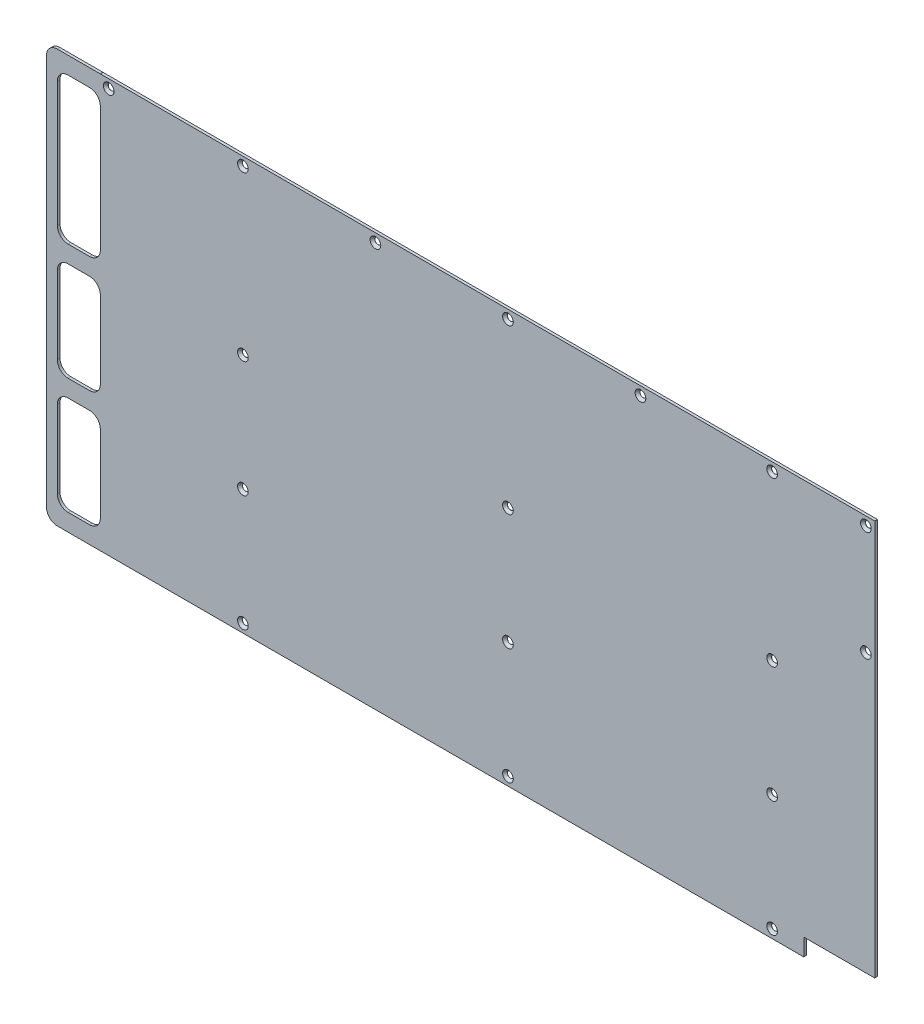
SolidWorks part; units mm, degrees
ref_plane "Front Plane" through (0, 0, 0) normal (0, 0, 1) x (1, 0, 0)
ref_plane "Top Plane" through (0, 0, 0) normal (0, 1, 0) x (1, 0, 0)
ref_plane "Right Plane" through (0, 0, 0) normal (1, 0, 0) x (0, 0, -1)
sketch "Model" plane through (0, 0, 0) normal (0, 0, 1) x (1, 0, 0)
  line L0 (0.1482, 0) -> (415.4382, 0)
  line L1 (415.4382, 0) -> (415.4382, 10.16)
  line L2 (415.4382, 10.16) -> (457.3482, 10.16)
  line L3 (457.3482, 10.16) -> (457.3482, 243.84)
  line L4 (457.3482, 243.84) -> (0.1482, 243.84)
  line L5 (0.1482, 243.84) -> (0.1482, 243.7765)
  line L6 (0.1482, 227.33) -> (0.1482, 153.67)
  line L7 (0.1482, 243.84) -> (-25.2518, 243.84)
  line L8 (0.1482, 243.84) -> (0.1482, 243.7765)
  line L9 (0.1482, 0) -> (-25.2518, 0)
  line L10 (-31.6018, 237.49) -> (-31.6018, 6.35)
  line L11 (-6.2018, 233.68) -> (-18.9018, 233.68)
  line L12 (0.1482, 233.68) -> (0.1482, 147.32)
  line L13 (-6.2018, 147.32) -> (-18.9018, 147.32)
  line L14 (-25.2518, 227.33) -> (-25.2518, 153.67)
  line L15 (-6.2018, 137.16) -> (-18.9018, 137.16)
  line L16 (0.1482, 130.81) -> (0.1482, 85.09)
  line L17 (-6.2018, 78.74) -> (-18.9018, 78.74)
  line L18 (-25.2518, 130.81) -> (-25.2518, 85.09)
  line L19 (-6.2018, 68.58) -> (-18.9018, 68.58)
  line L20 (0.1482, 62.23) -> (0.1482, 16.51)
  line L21 (-6.2018, 10.16) -> (-18.9018, 10.16)
  line L22 (-25.2518, 62.23) -> (-25.2518, 16.51)
  line L23 (0.1482, 233.68) -> (0.1482, 147.32)
  line L24 (0.1482, 137.16) -> (0.1482, 78.74)
  line L25 (0.1482, 137.16) -> (0.1482, 78.74)
  line L26 (0.1482, 68.58) -> (0.1482, 10.16)
  line L27 (0.1482, 68.58) -> (0.1482, 10.16)
  line L276 (452.12, 173.736) -> (452.12, 174.244)
  line L277 (451.866, 173.99) -> (452.374, 173.99)
  line L278 (452.12, 173.736) -> (452.12, 174.244)
  line L279 (451.866, 173.99) -> (452.374, 173.99)
  line L280 (452.12, 173.736) -> (452.12, 174.244)
  line L281 (451.866, 173.99) -> (452.374, 173.99)
  line L282 (452.12, 173.736) -> (452.12, 174.244)
  line L283 (451.866, 173.99) -> (452.374, 173.99)
  line L284 (452.12, 173.736) -> (452.12, 174.244)
  line L285 (451.866, 173.99) -> (452.374, 173.99)
  line L286 (452.12, 173.736) -> (452.12, 174.244)
  line L287 (451.866, 173.99) -> (452.374, 173.99)
  line L288 (452.12, 173.736) -> (452.12, 174.244)
  line L289 (451.866, 173.99) -> (452.374, 173.99)
  line L290 (452.12, 173.736) -> (452.12, 174.244)
  line L291 (451.866, 173.99) -> (452.374, 173.99)
  line L292 (452.12, 238.506) -> (452.12, 239.014)
  line L293 (451.866, 238.76) -> (452.374, 238.76)
  line L294 (452.12, 238.506) -> (452.12, 239.014)
  line L295 (451.866, 238.76) -> (452.374, 238.76)
  line L296 (452.12, 238.506) -> (452.12, 239.014)
  line L297 (451.866, 238.76) -> (452.374, 238.76)
  line L298 (452.12, 238.506) -> (452.12, 239.014)
  line L299 (451.866, 238.76) -> (452.374, 238.76)
  line L300 (452.12, 238.506) -> (452.12, 239.014)
  line L301 (451.866, 238.76) -> (452.374, 238.76)
  line L302 (452.12, 238.506) -> (452.12, 239.014)
  line L303 (451.866, 238.76) -> (452.374, 238.76)
  line L304 (452.12, 238.506) -> (452.12, 239.014)
  line L305 (451.866, 238.76) -> (452.374, 238.76)
  line L306 (452.12, 238.506) -> (452.12, 239.014)
  line L307 (451.866, 238.76) -> (452.374, 238.76)
  line L356 (5.08, 238.506) -> (5.08, 239.014)
  line L357 (4.826, 238.76) -> (5.334, 238.76)
  line L358 (5.08, 238.506) -> (5.08, 239.014)
  line L359 (4.826, 238.76) -> (5.334, 238.76)
  line L360 (5.08, 238.506) -> (5.08, 239.014)
  line L361 (4.826, 238.76) -> (5.334, 238.76)
  line L362 (5.08, 238.506) -> (5.08, 239.014)
  line L363 (4.826, 238.76) -> (5.334, 238.76)
  line L364 (5.08, 238.506) -> (5.08, 239.014)
  line L365 (4.826, 238.76) -> (5.334, 238.76)
  line L366 (5.08, 238.506) -> (5.08, 239.014)
  line L367 (4.826, 238.76) -> (5.334, 238.76)
  line L368 (5.08, 238.506) -> (5.08, 239.014)
  line L369 (4.826, 238.76) -> (5.334, 238.76)
  line L370 (5.08, 238.506) -> (5.08, 239.014)
  line L371 (4.826, 238.76) -> (5.334, 238.76)
  line L372 (84.328, 4.826) -> (84.328, 5.334)
  line L373 (84.074, 5.08) -> (84.582, 5.08)
  line L374 (84.328, 4.826) -> (84.328, 5.334)
  line L375 (84.074, 5.08) -> (84.582, 5.08)
  line L376 (84.328, 4.826) -> (84.328, 5.334)
  line L377 (84.074, 5.08) -> (84.582, 5.08)
  line L378 (84.328, 4.826) -> (84.328, 5.334)
  line L379 (84.074, 5.08) -> (84.582, 5.08)
  line L380 (84.328, 4.826) -> (84.328, 5.334)
  line L381 (84.074, 5.08) -> (84.582, 5.08)
  line L382 (84.328, 4.826) -> (84.328, 5.334)
  line L383 (84.074, 5.08) -> (84.582, 5.08)
  line L384 (84.328, 4.826) -> (84.328, 5.334)
  line L385 (84.074, 5.08) -> (84.582, 5.08)
  line L386 (84.328, 4.826) -> (84.328, 5.334)
  line L387 (84.074, 5.08) -> (84.582, 5.08)
  line L388 (84.328, 73.406) -> (84.328, 73.914)
  line L389 (84.074, 73.66) -> (84.582, 73.66)
  line L390 (84.328, 73.406) -> (84.328, 73.914)
  line L391 (84.074, 73.66) -> (84.582, 73.66)
  line L392 (84.328, 73.406) -> (84.328, 73.914)
  line L393 (84.074, 73.66) -> (84.582, 73.66)
  line L394 (84.328, 73.406) -> (84.328, 73.914)
  line L395 (84.074, 73.66) -> (84.582, 73.66)
  line L396 (84.328, 73.406) -> (84.328, 73.914)
  line L397 (84.074, 73.66) -> (84.582, 73.66)
  line L398 (84.328, 73.406) -> (84.328, 73.914)
  line L399 (84.074, 73.66) -> (84.582, 73.66)
  line L400 (84.328, 73.406) -> (84.328, 73.914)
  line L401 (84.074, 73.66) -> (84.582, 73.66)
  line L402 (84.328, 73.406) -> (84.328, 73.914)
  line L403 (84.074, 73.66) -> (84.582, 73.66)
  line L404 (84.328, 141.986) -> (84.328, 142.494)
  line L405 (84.074, 142.24) -> (84.582, 142.24)
  line L406 (84.328, 141.986) -> (84.328, 142.494)
  line L407 (84.074, 142.24) -> (84.582, 142.24)
  line L408 (84.328, 141.986) -> (84.328, 142.494)
  line L409 (84.074, 142.24) -> (84.582, 142.24)
  line L410 (84.328, 141.986) -> (84.328, 142.494)
  line L411 (84.074, 142.24) -> (84.582, 142.24)
  line L412 (84.328, 141.986) -> (84.328, 142.494)
  line L413 (84.074, 142.24) -> (84.582, 142.24)
  line L414 (84.328, 141.986) -> (84.328, 142.494)
  line L415 (84.074, 142.24) -> (84.582, 142.24)
  line L416 (84.328, 141.986) -> (84.328, 142.494)
  line L417 (84.074, 142.24) -> (84.582, 142.24)
  line L418 (84.328, 141.986) -> (84.328, 142.494)
  line L419 (84.074, 142.24) -> (84.582, 142.24)
  line L420 (84.328, 238.506) -> (84.328, 239.014)
  line L421 (84.074, 238.76) -> (84.582, 238.76)
  line L422 (84.328, 238.506) -> (84.328, 239.014)
  line L423 (84.074, 238.76) -> (84.582, 238.76)
  line L424 (84.328, 238.506) -> (84.328, 239.014)
  line L425 (84.074, 238.76) -> (84.582, 238.76)
  line L426 (84.328, 238.506) -> (84.328, 239.014)
  line L427 (84.074, 238.76) -> (84.582, 238.76)
  line L428 (84.328, 238.506) -> (84.328, 239.014)
  line L429 (84.074, 238.76) -> (84.582, 238.76)
  line L430 (84.328, 238.506) -> (84.328, 239.014)
  line L431 (84.074, 238.76) -> (84.582, 238.76)
  line L432 (84.328, 238.506) -> (84.328, 239.014)
  line L433 (84.074, 238.76) -> (84.582, 238.76)
  line L434 (84.328, 238.506) -> (84.328, 239.014)
  line L435 (84.074, 238.76) -> (84.582, 238.76)
  line L484 (162.56, 238.506) -> (162.56, 239.014)
  line L485 (162.306, 238.76) -> (162.814, 238.76)
  line L486 (162.56, 238.506) -> (162.56, 239.014)
  line L487 (162.306, 238.76) -> (162.814, 238.76)
  line L488 (162.56, 238.506) -> (162.56, 239.014)
  line L489 (162.306, 238.76) -> (162.814, 238.76)
  line L490 (162.56, 238.506) -> (162.56, 239.014)
  line L491 (162.306, 238.76) -> (162.814, 238.76)
  line L492 (162.56, 238.506) -> (162.56, 239.014)
  line L493 (162.306, 238.76) -> (162.814, 238.76)
  line L494 (162.56, 238.506) -> (162.56, 239.014)
  line L495 (162.306, 238.76) -> (162.814, 238.76)
  line L496 (162.56, 238.506) -> (162.56, 239.014)
  line L497 (162.306, 238.76) -> (162.814, 238.76)
  line L498 (162.56, 238.506) -> (162.56, 239.014)
  line L499 (162.306, 238.76) -> (162.814, 238.76)
  line L500 (240.7699, 4.827) -> (240.8141, 5.333)
  line L501 (240.539, 5.1021) -> (241.045, 5.0579)
  line L502 (240.7699, 4.827) -> (240.8141, 5.333)
  line L503 (240.539, 5.1021) -> (241.045, 5.0579)
  line L504 (240.7699, 4.827) -> (240.8141, 5.333)
  line L505 (240.539, 5.1021) -> (241.045, 5.0579)
  line L506 (240.7699, 4.827) -> (240.8141, 5.333)
  line L507 (240.539, 5.1021) -> (241.045, 5.0579)
  line L508 (240.7699, 4.827) -> (240.8141, 5.333)
  line L509 (240.539, 5.1021) -> (241.045, 5.0579)
  line L510 (240.7699, 4.827) -> (240.8141, 5.333)
  line L511 (240.539, 5.1021) -> (241.045, 5.0579)
  line L512 (240.7699, 4.827) -> (240.8141, 5.333)
  line L513 (240.539, 5.1021) -> (241.045, 5.0579)
  line L514 (240.7699, 4.827) -> (240.8141, 5.333)
  line L515 (240.539, 5.1021) -> (241.045, 5.0579)
  line L516 (240.792, 73.406) -> (240.792, 73.914)
  line L517 (240.538, 73.66) -> (241.046, 73.66)
  line L518 (240.792, 73.406) -> (240.792, 73.914)
  line L519 (240.538, 73.66) -> (241.046, 73.66)
  line L520 (240.792, 73.406) -> (240.792, 73.914)
  line L521 (240.538, 73.66) -> (241.046, 73.66)
  line L522 (240.792, 73.406) -> (240.792, 73.914)
  line L523 (240.538, 73.66) -> (241.046, 73.66)
  line L524 (240.792, 73.406) -> (240.792, 73.914)
  line L525 (240.538, 73.66) -> (241.046, 73.66)
  line L526 (240.792, 73.406) -> (240.792, 73.914)
  line L527 (240.538, 73.66) -> (241.046, 73.66)
  line L528 (240.792, 73.406) -> (240.792, 73.914)
  line L529 (240.538, 73.66) -> (241.046, 73.66)
  line L530 (240.792, 73.406) -> (240.792, 73.914)
  line L531 (240.538, 73.66) -> (241.046, 73.66)
  line L532 (240.792, 141.986) -> (240.792, 142.494)
  line L533 (240.538, 142.24) -> (241.046, 142.24)
  line L534 (240.792, 141.986) -> (240.792, 142.494)
  line L535 (240.538, 142.24) -> (241.046, 142.24)
  line L536 (240.792, 141.986) -> (240.792, 142.494)
  line L537 (240.538, 142.24) -> (241.046, 142.24)
  line L538 (240.792, 141.986) -> (240.792, 142.494)
  line L539 (240.538, 142.24) -> (241.046, 142.24)
  line L540 (240.792, 141.986) -> (240.792, 142.494)
  line L541 (240.538, 142.24) -> (241.046, 142.24)
  line L542 (240.792, 141.986) -> (240.792, 142.494)
  line L543 (240.538, 142.24) -> (241.046, 142.24)
  line L544 (240.792, 141.986) -> (240.792, 142.494)
  line L545 (240.538, 142.24) -> (241.046, 142.24)
  line L546 (240.792, 141.986) -> (240.792, 142.494)
  line L547 (240.538, 142.24) -> (241.046, 142.24)
  line L548 (240.792, 238.506) -> (240.792, 239.014)
  line L549 (240.538, 238.76) -> (241.046, 238.76)
  line L550 (240.792, 238.506) -> (240.792, 239.014)
  line L551 (240.538, 238.76) -> (241.046, 238.76)
  line L552 (240.792, 238.506) -> (240.792, 239.014)
  line L553 (240.538, 238.76) -> (241.046, 238.76)
  line L554 (240.792, 238.506) -> (240.792, 239.014)
  line L555 (240.538, 238.76) -> (241.046, 238.76)
  line L556 (240.792, 238.506) -> (240.792, 239.014)
  line L557 (240.538, 238.76) -> (241.046, 238.76)
  line L558 (240.792, 238.506) -> (240.792, 239.014)
  line L559 (240.538, 238.76) -> (241.046, 238.76)
  line L560 (240.792, 238.506) -> (240.792, 239.014)
  line L561 (240.538, 238.76) -> (241.046, 238.76)
  line L562 (240.792, 238.506) -> (240.792, 239.014)
  line L563 (240.538, 238.76) -> (241.046, 238.76)
  line L612 (319.024, 238.506) -> (319.024, 239.014)
  line L613 (318.77, 238.76) -> (319.278, 238.76)
  line L614 (319.024, 238.506) -> (319.024, 239.014)
  line L615 (318.77, 238.76) -> (319.278, 238.76)
  line L616 (319.024, 238.506) -> (319.024, 239.014)
  line L617 (318.77, 238.76) -> (319.278, 238.76)
  line L618 (319.024, 238.506) -> (319.024, 239.014)
  line L619 (318.77, 238.76) -> (319.278, 238.76)
  line L620 (319.024, 238.506) -> (319.024, 239.014)
  line L621 (318.77, 238.76) -> (319.278, 238.76)
  line L622 (319.024, 238.506) -> (319.024, 239.014)
  line L623 (318.77, 238.76) -> (319.278, 238.76)
  line L624 (319.024, 238.506) -> (319.024, 239.014)
  line L625 (318.77, 238.76) -> (319.278, 238.76)
  line L626 (319.024, 238.506) -> (319.024, 239.014)
  line L627 (318.77, 238.76) -> (319.278, 238.76)
  line L628 (396.748, 4.826) -> (396.748, 5.334)
  line L629 (396.494, 5.08) -> (397.002, 5.08)
  line L630 (396.748, 4.826) -> (396.748, 5.334)
  line L631 (396.494, 5.08) -> (397.002, 5.08)
  line L632 (396.748, 4.826) -> (396.748, 5.334)
  line L633 (396.494, 5.08) -> (397.002, 5.08)
  line L634 (396.748, 4.826) -> (396.748, 5.334)
  line L635 (396.494, 5.08) -> (397.002, 5.08)
  line L636 (396.748, 4.826) -> (396.748, 5.334)
  line L637 (396.494, 5.08) -> (397.002, 5.08)
  line L638 (396.748, 4.826) -> (396.748, 5.334)
  line L639 (396.494, 5.08) -> (397.002, 5.08)
  line L640 (396.748, 4.826) -> (396.748, 5.334)
  line L641 (396.494, 5.08) -> (397.002, 5.08)
  line L642 (396.748, 4.826) -> (396.748, 5.334)
  line L643 (396.494, 5.08) -> (397.002, 5.08)
  line L644 (396.748, 73.406) -> (396.748, 73.914)
  line L645 (396.494, 73.66) -> (397.002, 73.66)
  line L646 (396.748, 73.406) -> (396.748, 73.914)
  line L647 (396.494, 73.66) -> (397.002, 73.66)
  line L648 (396.748, 73.406) -> (396.748, 73.914)
  line L649 (396.494, 73.66) -> (397.002, 73.66)
  line L650 (396.748, 73.406) -> (396.748, 73.914)
  line L651 (396.494, 73.66) -> (397.002, 73.66)
  line L652 (396.748, 73.406) -> (396.748, 73.914)
  line L653 (396.494, 73.66) -> (397.002, 73.66)
  line L654 (396.748, 73.406) -> (396.748, 73.914)
  line L655 (396.494, 73.66) -> (397.002, 73.66)
  line L656 (396.748, 73.406) -> (396.748, 73.914)
  line L657 (396.494, 73.66) -> (397.002, 73.66)
  line L658 (396.748, 73.406) -> (396.748, 73.914)
  line L659 (396.494, 73.66) -> (397.002, 73.66)
  line L660 (396.748, 141.986) -> (396.748, 142.494)
  line L661 (396.494, 142.24) -> (397.002, 142.24)
  line L662 (396.748, 141.986) -> (396.748, 142.494)
  line L663 (396.494, 142.24) -> (397.002, 142.24)
  line L664 (396.748, 141.986) -> (396.748, 142.494)
  line L665 (396.494, 142.24) -> (397.002, 142.24)
  line L666 (396.748, 141.986) -> (396.748, 142.494)
  line L667 (396.494, 142.24) -> (397.002, 142.24)
  line L668 (396.748, 141.986) -> (396.748, 142.494)
  line L669 (396.494, 142.24) -> (397.002, 142.24)
  line L670 (396.748, 141.986) -> (396.748, 142.494)
  line L671 (396.494, 142.24) -> (397.002, 142.24)
  line L672 (396.748, 141.986) -> (396.748, 142.494)
  line L673 (396.494, 142.24) -> (397.002, 142.24)
  line L674 (396.748, 141.986) -> (396.748, 142.494)
  line L675 (396.494, 142.24) -> (397.002, 142.24)
  line L676 (396.748, 238.506) -> (396.748, 239.014)
  line L677 (396.494, 238.76) -> (397.002, 238.76)
  line L678 (396.748, 238.506) -> (396.748, 239.014)
  line L679 (396.494, 238.76) -> (397.002, 238.76)
  line L680 (396.748, 238.506) -> (396.748, 239.014)
  line L681 (396.494, 238.76) -> (397.002, 238.76)
  line L682 (396.748, 238.506) -> (396.748, 239.014)
  line L683 (396.494, 238.76) -> (397.002, 238.76)
  line L684 (396.748, 238.506) -> (396.748, 239.014)
  line L685 (396.494, 238.76) -> (397.002, 238.76)
  line L686 (396.748, 238.506) -> (396.748, 239.014)
  line L687 (396.494, 238.76) -> (397.002, 238.76)
  line L688 (396.748, 238.506) -> (396.748, 239.014)
  line L689 (396.494, 238.76) -> (397.002, 238.76)
  line L690 (396.748, 238.506) -> (396.748, 239.014)
  line L691 (396.494, 238.76) -> (397.002, 238.76)
  arc A0 (0.1482, 16.51) -> (-6.2018, 10.16) centre (-6.2018, 16.51) cw
  circle A1 centre (415.4382, 0) radius 0.0635
  circle A2 centre (415.4382, 10.16) radius 0.0635
  circle A3 centre (457.3482, 10.16) radius 0.0635
  circle A4 centre (457.3482, 243.84) radius 0.0635
  circle A5 centre (0.1482, 243.84) radius 0.0635
  arc A6 (-6.2018, 68.58) -> (0.1482, 62.23) centre (-6.2018, 62.23) cw
  arc A7 (0.1482, 85.09) -> (-6.2018, 78.74) centre (-6.2018, 85.09) cw
  arc A8 (-31.6018, 6.35) -> (-25.2518, 0) centre (-25.2518, 6.35) ccw
  arc A9 (-25.2518, 16.51) -> (-18.9018, 10.16) centre (-18.9018, 16.51) ccw
  arc A10 (-25.2518, 62.23) -> (-18.9018, 68.58) centre (-18.9018, 62.23) cw
  arc A11 (-25.2518, 85.09) -> (-18.9018, 78.74) centre (-18.9018, 85.09) ccw
  arc A12 (-25.2518, 130.81) -> (-18.9018, 137.16) centre (-18.9018, 130.81) cw
  arc A13 (-25.2518, 153.67) -> (-18.9018, 147.32) centre (-18.9018, 153.67) ccw
  arc A14 (-25.2518, 243.84) -> (-31.6018, 237.49) centre (-25.2518, 237.49) ccw
  arc A15 (-25.2518, 227.33) -> (-18.9018, 233.68) centre (-18.9018, 227.33) cw
  arc A16 (0.1482, 130.81) -> (-6.2018, 137.16) centre (-6.2018, 130.81) ccw
  arc A17 (0.1482, 153.67) -> (-6.2018, 147.32) centre (-6.2018, 153.67) cw
  arc A18 (0.1482, 227.33) -> (-6.2018, 233.68) centre (-6.2018, 227.33) ccw
  circle A66 centre (5.08, 238.76) radius 1.8288
  circle A67 centre (84.328, 238.76) radius 1.8288
  circle A68 centre (162.56, 238.76) radius 1.8288
  circle A69 centre (240.792, 238.76) radius 1.8288
  circle A70 centre (319.024, 238.76) radius 1.8288
  circle A71 centre (396.748, 238.76) radius 1.8288
  circle A72 centre (452.12, 238.76) radius 1.8288
  circle A73 centre (452.12, 173.99) radius 1.8288
  circle A74 centre (396.748, 142.24) radius 1.8288
  circle A76 centre (240.792, 142.24) radius 1.8288
  circle A78 centre (84.328, 142.24) radius 1.8288
  circle A81 centre (84.328, 73.66) radius 1.8288
  circle A83 centre (240.792, 73.66) radius 1.8288
  circle A85 centre (396.748, 73.66) radius 1.8288
  circle A86 centre (396.748, 5.08) radius 1.8288
  circle A88 centre (240.792, 5.08) radius 1.8288
  circle A90 centre (84.328, 5.08) radius 1.8288
  point P38 (-25.2518, 10.16)
  point P41 (-25.2518, 68.58)
  point P44 (-25.2518, 78.74)
  point P47 (-25.2518, 137.16)
  point P50 (-25.2518, 147.32)
  point P53 (-31.6018, 243.84)
  point P56 (-25.2518, 233.68)
  dimension "D1" = 391.668
  dimension "D22" = 31.75
  dimension "D23" = 6.35
  dimension "D16" = 6.35
  dimension "D2" = 77.724
  dimension "D3" = 78.232
  dimension "D4" = 78.232
  dimension "D5" = 78.232
  dimension "D6" = 79.248
  dimension "D7" = 96.52
  dimension "D8" = 68.58
  dimension "D9" = 68.58
  dimension "D10" = 68.58
  dimension "D11" = 68.58
  dimension "D12" = 96.52
  dimension "D13" = 96.52
  dimension "D14" = 68.58
  dimension "D15" = 68.58
  dimension "D24" = 25.4
  dimension "D25" = 25.4
  dimension "D26" = 25.4
  dimension "D27" = 86.36
  dimension "D28" = 58.42
  dimension "D29" = 58.42
  dimension "D30" = 10.16
  dimension "D31" = 10.16
  dimension "D32" = 10.16
extrude "Boss-Extrude2" add sketch "Model" along normal blind 1.5875
hole_wizard "CSK for #6 Flat Head Machine Screw2" positions "Sketch5" profile "Sketch4" countersink size "#6" standard "ANSI Inch" end condition through all
sketch "Sketch5" plane through (0, 0, 1.5875) normal (0, 0, 1) x (1, 0, 0)
  point P2 (5.08, 238.76)
  point P5 (84.328, 238.76)
  point P8 (162.56, 238.76)
  point P11 (240.792, 238.76)
  point P14 (319.024, 238.76)
  point P17 (396.748, 238.76)
  point P20 (452.12, 238.76)
  point P23 (452.12, 173.99)
  point P26 (396.748, 142.24)
  point P29 (396.748, 73.66)
  point P32 (396.748, 5.08)
  point P35 (240.792, 5.08)
  point P38 (240.792, 73.66)
  point P41 (240.792, 142.24)
  point P44 (84.328, 142.24)
  point P47 (84.328, 73.66)
  point P50 (84.328, 5.08)
sketch "Sketch4" plane through (5.08, 238.76, 1.5875) normal (1, 0, 0) x (0, -1, 0)
  line L0 (0, 0) -> (0, 1.5875)
  line L1 (0, 1.5875) -> (1.8288, 1.5875)
  line L2 (1.8288, 1.5875) -> (1.8288, 1.5194)
  line L3 (1.8288, 1.5194) -> (3.1496, 0)
  line L5 (3.1496, 0) -> (0, 0)
  line L6 (-1.8288, 1.5194) -> (-3.1496, 0) construction
  line L11 (0, -6.35) -> (0, 107.95) construction
  dimension "Thru Hole Dia." = 3.6576
  dimension "Thru Hole Depth" = 1.5875
  dimension "Near C'Sink Dia." = 6.2992
  dimension "Near C'Sink Angle" = 82
